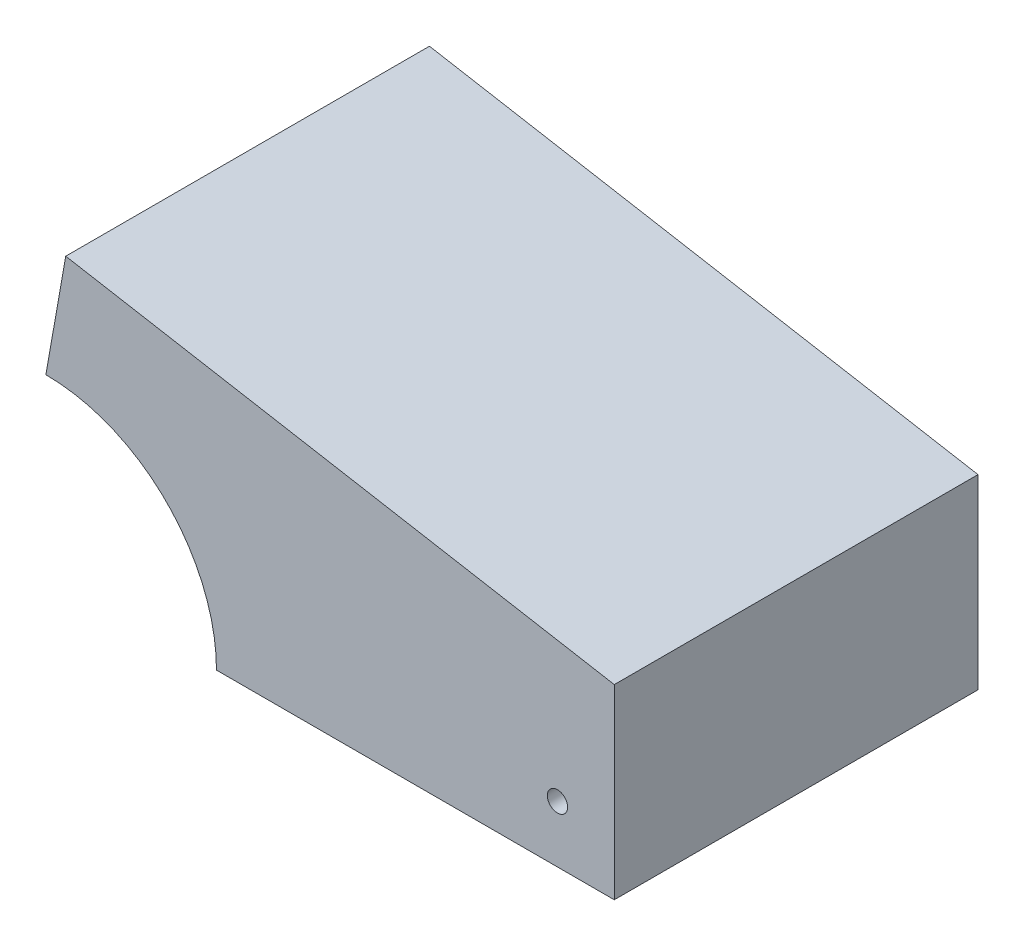
SolidWorks part; units mm, degrees
ref_plane "Front Plane" through (0, 0, 0) normal (0, 0, 1) x (1, 0, 0)
ref_plane "Top Plane" through (0, 0, 0) normal (0, 1, 0) x (1, 0, 0)
ref_plane "Right Plane" through (0, 0, 0) normal (1, 0, 0) x (0, 0, -1)
sketch "Sketch2" plane through (0, 0, 0) normal (0, 0, 1) x (1, 0, 0)
  line L0 (0, 0) -> (75.2886, 0)
  line L1 (75.2886, 0) -> (56.4664, 32.6009)
  line L2 (0, -65.2018) -> (-81.9123, -65.2018) construction
  line L3 (-11.3222, -64.2112) -> (-111.3786, -46.5686)
  line L4 (56.4664, 32.6009) -> (37.4164, 65.5965)
  arc A0 (56.4664, 32.6009) -> (-11.3222, -64.2112) centre (0, 0) cw
  circle A1 centre (0, 0) radius 45.212 construction
  point P11 (-11.3222, -64.2112)
  dimension "D3" = 90.424
  dimension "D1" = 65.2018
  dimension "D2" = 60
  dimension "D4" = 10
  dimension "D5" = 38.1
  dimension "D6" = 101.6
sketch3d "3DSketch1"
  line L0 (-114.819, -66.0796, 0) -> (-111.3786, -46.5686, 0) construction
  line L1 (-117.0243, -78.5867, -20.32) -> (-114.819, -66.0796, -20.32)
  line L2 (-117.0243, -78.5867, -20.32) -> (-117.0243, -78.5867, 20.32)
  line L3 (-117.0243, -78.5867, 20.32) -> (-114.819, -66.0796, 20.32)
  line L4 (-114.819, -66.0796, -20.32) -> (-114.819, -66.0796, 20.32)
  line L5 (-117.0243, -78.5867, -20.32) -> (-114.819, -66.0796, 20.32) construction
  line L6 (-117.0243, -78.5867, 20.32) -> (-114.819, -66.0796, -20.32) construction
  line L7 (-11.3222, -64.2112, 0) -> (-111.3786, -46.5686, 0) construction
  line L8 (0, -65.2018, 0) -> (-81.9123, -65.2018, 0) construction
  point P4 (-115.9216, -72.3331, 0)
  dimension "D1" = 12.7
  dimension "D2" = 40.64
  dimension "D3" = 19.812
sweep "Sweep3" add profiles "3DSketch1" path "Sketch2"
sketch "Sketch5" plane through (0, 0, 20.32) normal (0, 0, 1) x (1, 0, 0)
  line L0 (-117.0243, -78.5867) -> (-117.0243, -97.7138)
  line L1 (-117.0243, -97.7138) -> (97.7138, -97.7138)
  line L2 (97.7138, -97.7138) -> (97.7138, 81.8525)
  line L3 (97.7138, 81.8525) -> (65.5726, 81.8525)
  line L4 (-117.0243, -78.5867) -> (-16.9678, -96.2293)
  line L5 (84.6226, 48.8569) -> (65.5726, 81.8525)
  arc A0 (-16.9678, -96.2293) -> (84.6226, 48.8569) centre (0, 0) ccw construction
  arc A1 (-16.9678, -96.2293) -> (84.6226, 48.8569) centre (0, 0) ccw
  line M7 (-117.0243, -78.5867) -> (-16.9678, -96.2293)
extrude "Boss-Extrude1" add sketch "Sketch5" against normal up to surface (40.64 mm away) contours A1 L0 L1 M7 | A1 L1 L2 | A1 L2 L3 L5 up to face at (-65.8934, -81.1545, -20.32)
sketch "Sketch6" plane through (0, 0, 20.32) normal (0, 0, 1) x (1, 0, 0)
  circle A0 centre (91.3638, -91.3638) radius 1.1303 construction
  circle A1 centre (-41.9735, -91.3638) radius 1.1303 construction
  circle A2 centre (91.3638, -91.3638) radius 1.1303
  circle A3 centre (-41.9735, -91.3638) radius 1.1303
extrude "Cut-Extrude1" cut sketch "Sketch6" against normal through all
sketch "Sketch7" plane through (0, 0, 20.32) normal (0, 0, 1) x (1, 0, 0)
  line L0 (-117.0243, -97.7138) -> (97.7138, -97.7138) construction
  line L1 (-53.5243, -97.7138) -> (141.999, -97.7138)
  line L2 (-53.5243, -97.7138) -> (-53.5243, 97.8095)
  line L3 (-53.5243, 97.8095) -> (141.999, 97.8095)
  line L4 (141.999, -97.7138) -> (141.999, 97.8095)
  line L5 (-53.5243, -97.7138) -> (141.999, 97.8095) construction
  line L6 (-53.5243, 97.8095) -> (141.999, -97.7138) construction
  line L7 (-117.0243, -78.5867) -> (-117.0243, -97.7138) construction
  point P4 (44.2374, 0.0479)
  dimension "D1" = 63.5
extrude "Cut-Extrude2" cut sketch "Sketch7" against normal through all
sketch "Sketch8" plane through (0, 0, 20.32) normal (0, 0, 1) x (1, 0, 0)
  line L0 (-117.0243, -97.7138) -> (-53.5243, -97.7138) construction
  line L1 (-53.5243, -76.8875) -> (-53.5243, -97.7138) construction
  circle A0 centre (-59.8743, -91.3638) radius 1.1303
  dimension "D3" = 2.2606
  dimension "D1" = 6.35
  dimension "D2" = 6.35
extrude "Cut-Extrude3" cut sketch "Sketch8" against normal through all
sketch "Sketch9" plane through (0, 0, 20.32) normal (0, 0, 1) x (1, 0, 0)
  circle A0 centre (-117.0243, -97.7138) radius 19.05
  dimension "D1" = 38.1
extrude "Cut-Extrude4" cut sketch "Sketch9" against normal through all
